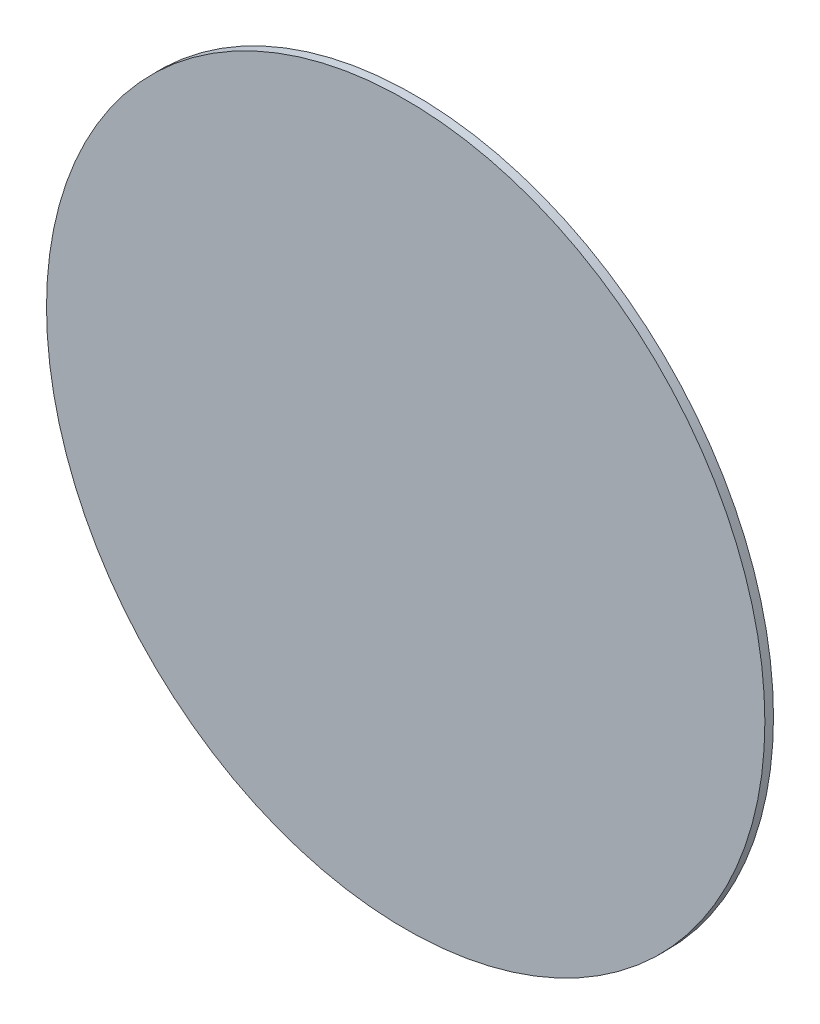
SolidWorks part; units mm, degrees
material "1060 Alloy"
ref_plane "Front Plane" through (0, 0, 0) normal (0, 0, 1) x (1, 0, 0)
ref_plane "Top Plane" through (0, 0, 0) normal (0, 1, 0) x (1, 0, 0)
ref_plane "Right Plane" through (0, 0, 0) normal (1, 0, 0) x (0, 0, -1)
sketch "Sketch1" plane through (0, 0, 0) normal (0, 0, 1) x (1, 0, 0)
  circle A0 centre (0, 0) radius 125
  point P2 (15.1929, -29.649)
  dimension "D1" = 250
extrude "Boss-Extrude1" add sketch "Sketch1" along normal blind 3
